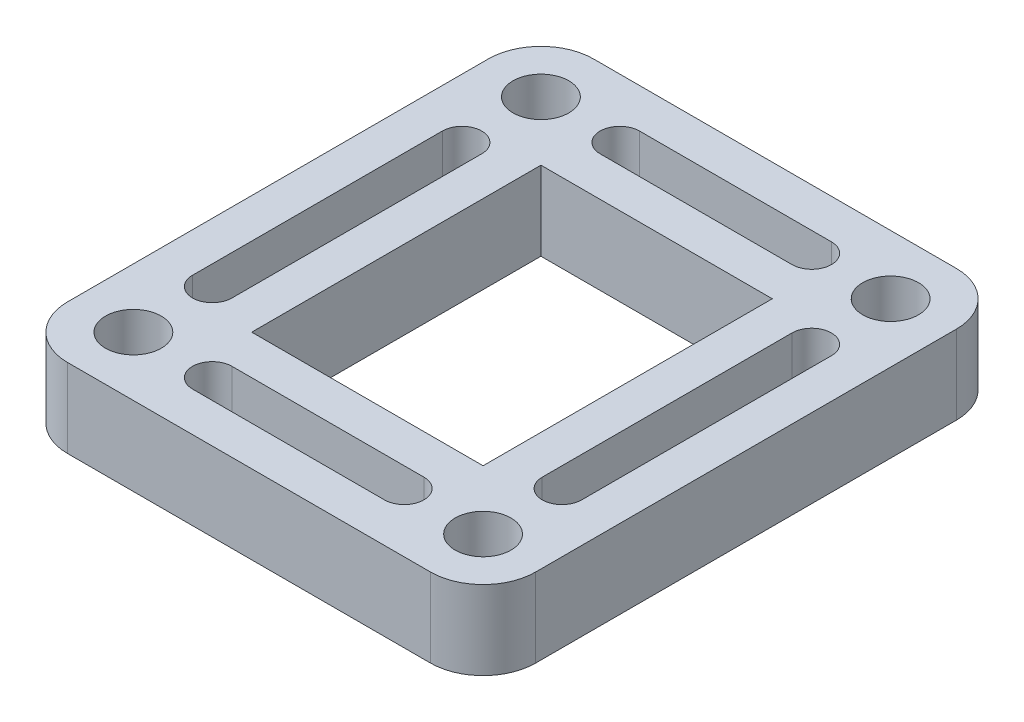
SolidWorks part; units mm, degrees
ref_plane "Front Plane" through (0, 0, 0) normal (0, 0, 1) x (1, 0, 0)
ref_plane "Top Plane" through (0, 0, 0) normal (0, 1, 0) x (1, 0, 0)
ref_plane "Right Plane" through (0, 0, 0) normal (1, 0, 0) x (0, 0, -1)
sketch "Sketch1" plane through (0, 0, 0) normal (0, 1, 0) x (1, 0, 0)
  line L0 (-22.606, -20.32) -> (-22.606, 20.32)
  line L1 (-11.176, -13.97) -> (11.176, -13.97)
  line L2 (-11.176, -13.97) -> (-11.176, 13.97)
  line L3 (-11.176, 13.97) -> (11.176, 13.97)
  line L4 (11.176, -13.97) -> (11.176, 13.97)
  line L5 (-11.176, -13.97) -> (11.176, 13.97) construction
  line L6 (-11.176, 13.97) -> (11.176, -13.97) construction
  line L7 (-17.526, 25.4) -> (17.526, 25.4)
  line L8 (22.606, -20.32) -> (22.606, 20.32)
  line L9 (-17.526, -25.4) -> (17.526, -25.4)
  line L10 (16.891, 12.065) -> (16.891, -12.065) construction
  line L11 (18.796, 12.065) -> (18.796, -12.065)
  line L12 (14.986, 12.065) -> (14.986, -12.065)
  line L13 (0, 0) -> (0, -6.1659) construction
  line L14 (-9.271, -19.685) -> (9.271, -19.685) construction
  line L15 (-9.271, -17.78) -> (9.271, -17.78)
  line L16 (-9.271, -21.59) -> (9.271, -21.59)
  line L17 (0, 0) -> (28.3221, 0) construction
  line L18 (-9.271, 19.685) -> (9.271, 19.685) construction
  line L19 (-9.271, 17.78) -> (9.271, 17.78)
  line L20 (-9.271, 21.59) -> (9.271, 21.59)
  line L21 (-16.891, 12.065) -> (-16.891, -12.065) construction
  line L24 (-22.606, -25.4) -> (-22.606, 25.4) construction
  line L25 (-22.606, -25.4) -> (22.606, -25.4) construction
  line L26 (22.606, -25.4) -> (22.606, 25.4) construction
  line L27 (-22.606, 25.4) -> (22.606, 25.4) construction
  line L28 (-18.796, 12.065) -> (-18.796, -12.065)
  line L29 (-14.986, 12.065) -> (-14.986, -12.065)
  arc A0 (18.796, 12.065) -> (14.986, 12.065) centre (16.891, 12.065) ccw
  arc A1 (14.986, -12.065) -> (18.796, -12.065) centre (16.891, -12.065) ccw
  arc A2 (-9.271, -17.78) -> (-9.271, -21.59) centre (-9.271, -19.685) ccw
  arc A3 (9.271, -21.59) -> (9.271, -17.78) centre (9.271, -19.685) ccw
  arc A4 (-9.271, 17.78) -> (-9.271, 21.59) centre (-9.271, 19.685) cw
  arc A5 (9.271, 21.59) -> (9.271, 17.78) centre (9.271, 19.685) cw
  circle A9 centre (16.891, 19.685) radius 2.6941
  circle A11 centre (16.891, -19.685) radius 2.6941
  arc A14 (-22.606, -20.32) -> (-17.526, -25.4) centre (-17.526, -20.32) ccw
  arc A15 (17.526, -25.4) -> (22.606, -20.32) centre (17.526, -20.32) ccw
  arc A16 (22.606, 20.32) -> (17.526, 25.4) centre (17.526, 20.32) ccw
  arc A17 (-22.606, 20.32) -> (-17.526, 25.4) centre (-17.526, 20.32) cw
  circle A18 centre (-16.891, -19.685) radius 2.6941
  arc A19 (-18.796, 12.065) -> (-14.986, 12.065) centre (-16.891, 12.065) cw
  arc A20 (-14.986, -12.065) -> (-18.796, -12.065) centre (-16.891, -12.065) cw
  circle A21 centre (-16.891, 19.685) radius 2.6941
  point P0 (0, 0)
  point P12 (16.891, 0)
  point P18 (0, -19.685)
  point P19 (0, 0)
  point P26 (-11.176, -19.685)
  point P27 (16.891, -13.97)
  point P29 (16.891, 13.97)
  point P30 (11.176, -19.685)
  point P34 (0, 19.685)
  point P43 (-16.891, 0)
  dimension "D6" = 22.352
  dimension "D7" = 27.94
  dimension "D8" = 5.08
  dimension "D1" = 22.352
  dimension "D2" = 27.94
  dimension "D4" = 3.81
  dimension "D5" = 3.81
  dimension "D3" = 11.43
extrude "Boss-Extrude1" add sketch "Sketch1" along normal blind 7.62
